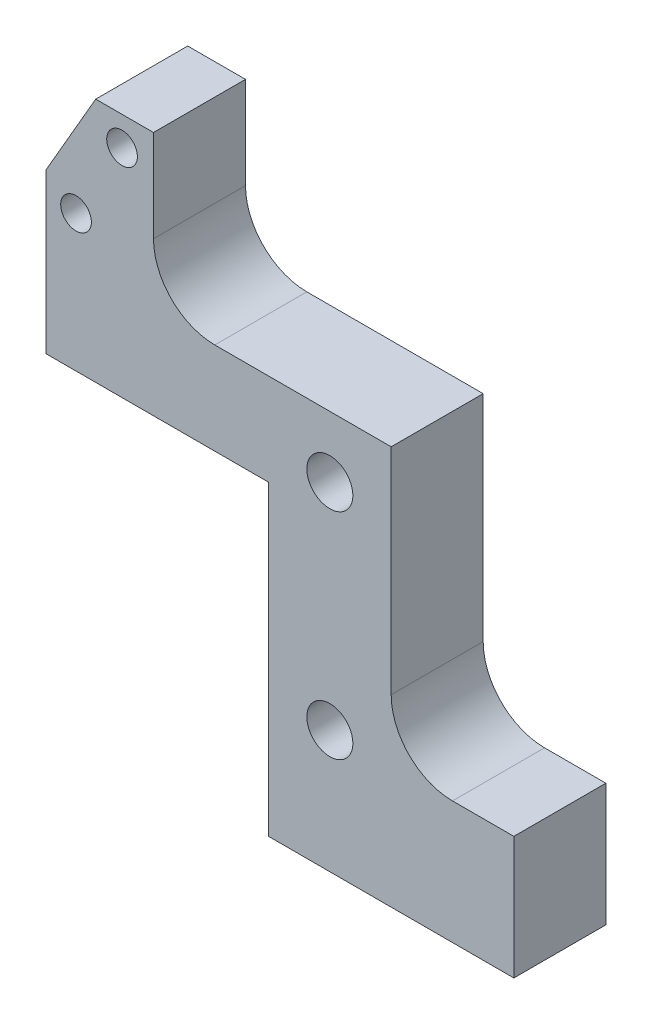
SolidWorks part; units mm, degrees
ref_plane "Front Plane" through (0, 0, 0) normal (0, 0, 1) x (1, 0, 0)
ref_plane "Top Plane" through (0, 0, 0) normal (0, 1, 0) x (1, 0, 0)
ref_plane "Right Plane" through (0, 0, 0) normal (1, 0, 0) x (0, 0, -1)
sketch "Sketch1" plane through (0, 0, 0) normal (0, 0, 1) x (1, 0, 0)
  line L0 (-27.2668, 36) -> (-30.5, 30.4)
  line L1 (0, 0) -> (-16, 0)
  line L2 (0, 0) -> (0, 8)
  line L3 (0, 8) -> (-8, 8)
  line L4 (-16, 0) -> (-16, 8)
  line L6 (-16, 8) -> (-16, 20)
  line L7 (-16, 26) -> (-8, 26)
  line L8 (-8, 8) -> (-8, 26)
  line L9 (-16, 26) -> (-23.5, 26)
  line L11 (-16, 20) -> (-30.5, 20)
  line L12 (-30.5, 26) -> (-30.5, 20)
  line L14 (-30.5, 26) -> (-30.5, 30.4)
  line L15 (-27.2668, 36) -> (-23.5, 36)
  line L16 (-23.5, 26) -> (-23.5, 36)
  circle A0 centre (-28.55, 28.91) radius 1
  circle A1 centre (-25.55, 34.1062) radius 1
  dimension "D11" = 1.95
  dimension "D15" = 2
  dimension "D16" = 2
  dimension "D1" = 16
  dimension "D2" = 8
  dimension "D3" = 18
  dimension "D4" = 8
  dimension "D5" = 20
  dimension "D6" = 14.5
  dimension "D7" = 7
  dimension "D8" = 10
  dimension "D9" = 30
  dimension "D10" = 5.6
  dimension "D12" = 7.09
  dimension "D14" = 6
extrude "Boss-Extrude1" add sketch "Sketch1" along normal blind 6
fillet "Fillet1" radius 4 1 edges at (-23.5, 26, 3)
fillet "Fillet2" radius 4 1 edges at (-8, 8, 3)
hole_wizard "M3x0.5 Tapped Hole1" positions "Sketch5" profile "Sketch4" tap size "M3x0.5" standard "ANSI Metric"
sketch "Sketch5" plane through (0, 0, 0) normal (0, -1, 0) x (-1, 0, 0)
  line L0 (0, -6) -> (0, 0) construction
  line L2 (16, 0) -> (0, 0) construction
  point P0 (13, -3)
  point P2 (3, -3)
  dimension "D1" = 3
  dimension "D2" = 13
  dimension "D3" = 3
sketch "Sketch4" plane through (-13, 0, 3) normal (1, 0, 0) x (0, 0, -1)
  line L0 (0, 0) -> (0, 4.7511)
  line L1 (0, 4.7511) -> (1.25, 4)
  line L2 (1.25, 4) -> (1.25, 0.275)
  line L3 (1.25, 0.275) -> (1.525, 0)
  line L5 (1.525, 0) -> (0, 0)
  line L6 (-1.25, 0.275) -> (-1.525, 0) construction
  line L10 (0, 4.7511) -> (-1.25, 4) construction
  line L11 (0, -6.35) -> (0, 107.95) construction
  dimension "Tap Drill Dia." = 2.5
  dimension "Tap Drill Depth" = 4
  dimension "Near C'Sink Dia." = 3.05
  dimension "Near C'Sink Angle" = 90
  dimension "Drill Angle" = 118
cosmetic thread "Hole Thread1" parameters "D1"=4, "D2"=3
cosmetic thread "Hole Thread2" parameters "D1"=4, "D2"=3
hole_wizard "Ø2.0 (2) Diameter Hole1" positions "Sketch7" profile "Sketch6" hole size "Ø2.0" standard "ANSI Metric"
sketch "Sketch7" plane through (0, 0, 0) normal (0, -1, 0) x (-1, 0, 0)
  line L0 (16, 0) -> (0, 0) construction
  line L1 (0, -6) -> (0, 0) construction
  point P0 (8, -3)
  dimension "D1" = 3
  dimension "D2" = 8
sketch "Sketch6" plane through (-8, 0, 3) normal (1, 0, 0) x (0, 0, -1)
  line L0 (0, 0) -> (0, 3.6009)
  line L1 (0, 3.6009) -> (1, 3)
  line L2 (1, 3) -> (1, 0)
  line L5 (1, 0) -> (0, 0)
  line L10 (0, 3.6009) -> (-1, 3) construction
  line L11 (0, -6.35) -> (0, 107.95) construction
  dimension "Hole Dia." = 2
  dimension "Hole Depth" = 3
  dimension "Drill Angle" = 118
sketch "Sketch8" plane through (0, 0, 0) normal (0, 0, -1) x (-1, 0, 0)
  line L1 (0, 8) -> (4, 8) construction
  line L2 (0, 0) -> (0, 8) construction
  line L3 (16, 0) -> (0, 0) construction
  circle A0 centre (12, 22) radius 3
  circle A1 centre (12, 8) radius 3
  dimension "D2" = 6
  dimension "D3" = 6
  dimension "D1" = 14
  dimension "D4" = 12
  dimension "D5" = 12
  dimension "D6" = 8
extrude "Cut-Extrude1" cut sketch "Sketch8" against normal blind 3
sketch "Sketch9" plane through (0, 0, 3) normal (0, 0, -1) x (-1, 0, 0)
  circle A0 centre (12, 22) radius 1.5
  circle A1 centre (12, 8) radius 1.5
  dimension "D1" = 3
  dimension "D2" = 3
extrude "Cut-Extrude2" cut sketch "Sketch9" against normal through all
